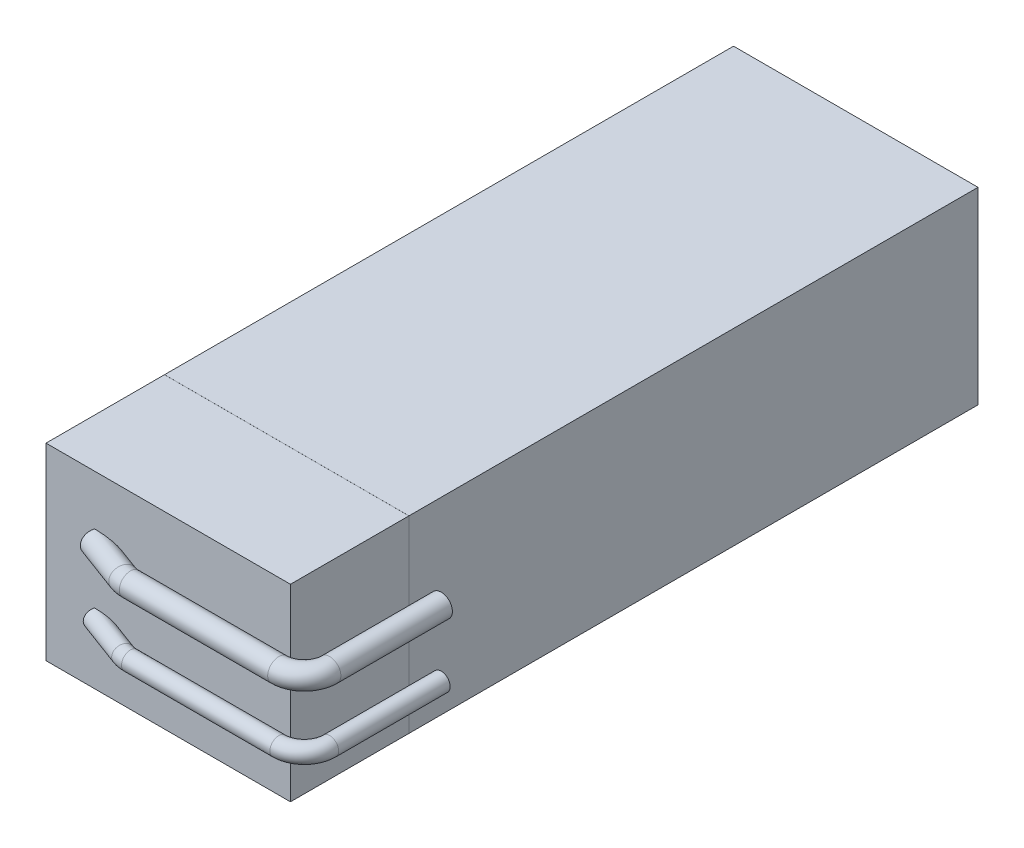
SolidWorks part; units mm, degrees
ref_plane "Plan de face" through (0, 0, 0) normal (0, 0, 1) x (1, 0, 0)
ref_plane "Plan de dessus" through (0, 0, 0) normal (0, 1, 0) x (1, 0, 0)
ref_plane "Plan de droite" through (0, 0, 0) normal (1, 0, 0) x (0, 0, -1)
sketch "Esquisse1" plane through (0, 0, 0) normal (1, 0, 0) x (0, 0, -1)
  line L1 (0, 0) -> (-135, 0)
  line L2 (0, 0) -> (0, 37)
  line L3 (0, 37) -> (-135, 37)
  line L4 (-135, 0) -> (-135, 37)
  dimension "D1" = 135
  dimension "D2" = 37
extrude "Boss.-Extru.1" add sketch "Esquisse1" along normal blind 48
ref_plane "Plan1" through (0, 12, 0) normal (0, -1, 0) x (-1, 0, 0)
ref_plane "Plan2" through (0, 25, 0) normal (0, -1, 0) x (-1, 0, 0)
sketch "Esquisse2" plane through (0, 12, 0) normal (0, -1, 0) x (-1, 0, 0)
  line L0 (-20.2021, -138.6272) -> (-49.3424, -138.6272)
  line L1 (-54.3424, -133.6272) -> (-54.3424, -111.7321)
  line L2 (-18.4574, -138.3129) -> (-9.5598, -135)
  line L3 (-48, -135) -> (0, -135) construction
  arc A0 (-54.3424, -133.6272) -> (-49.3424, -138.6272) centre (-49.3424, -133.6272) ccw
  arc A1 (-20.2021, -138.6272) -> (-18.4574, -138.3129) centre (-20.2021, -133.6272) ccw
  point P2 (0, 0)
  point P5 (0, 0)
  point P6 (-9.5598, -135)
  dimension "D1" = 5
  dimension "D2" = 5
ref_plane "Plan3" through (0, 0, 111.7321) normal (0, 0, -1) x (-1, 0, 0)
sketch "Esquisse3" plane through (0, 0, 111.7321) normal (0, 0, -1) x (-1, 0, 0)
  circle A0 centre (-54.3424, 12) radius 1.75
  circle A1 centre (-54.3424, 25) radius 2.1877
  dimension "D1" = 3.5
  dimension "D2" = 13
sweep "Balayage1" add profiles "Esquisse3" path "Esquisse2"
sketch "Esquisse4" plane through (0, 0, 111.7321) normal (0, 0, -1) x (-1, 0, 0)
  line L1 (0, 0) -> (-48, 0)
  line L2 (0, 0) -> (0, 37)
  line L3 (0, 37) -> (-48, 37)
  line L4 (-48, 0) -> (-48, 37)
  point P5 (0, 0)
extrude "Enlèv. mat.-Extru.1" cut sketch "Esquisse4" against normal blind 0.01
ref_plane "Plan4" through (24, 0, 0) normal (1, 0, 0) x (0, 0, -1)
